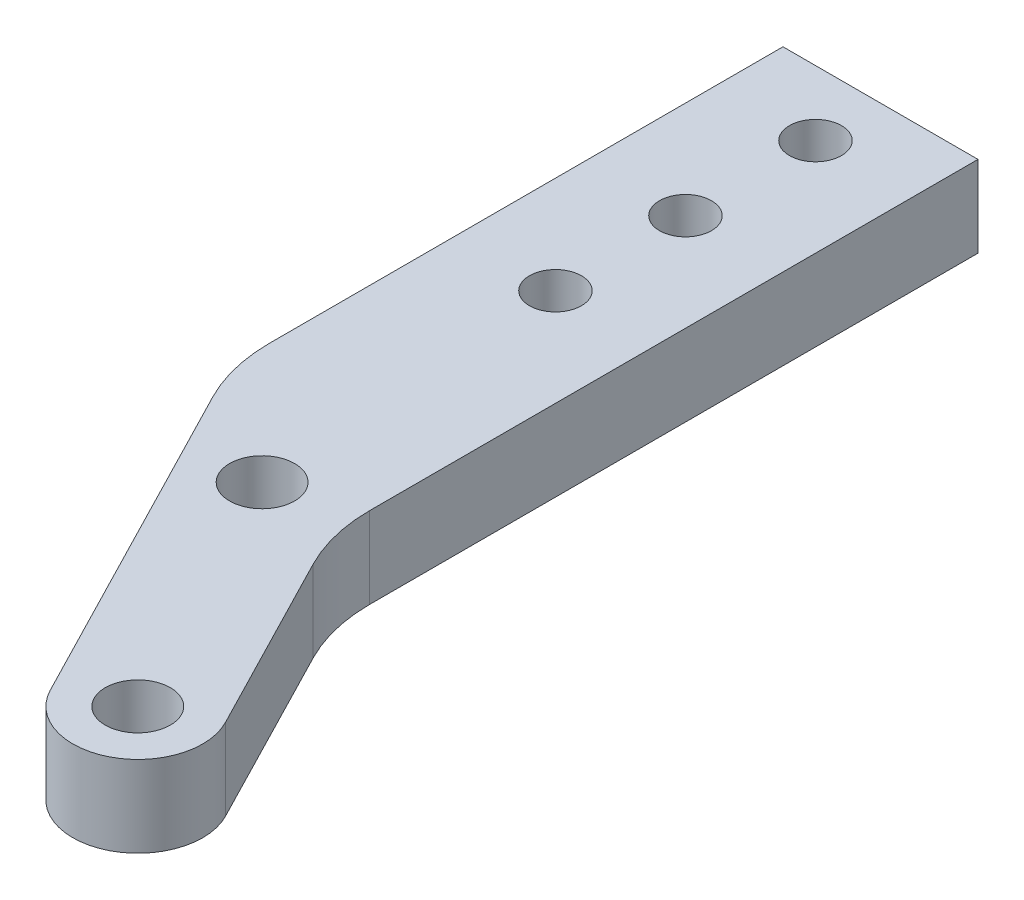
SolidWorks part; units mm, degrees
material "ABS"
ref_plane "Спереди" through (0, 0, 0) normal (0, 0, 1) x (1, 0, 0)
ref_plane "Сверху" through (0, 0, 0) normal (0, 1, 0) x (1, 0, 0)
ref_plane "Справа" through (0, 0, 0) normal (1, 0, 0) x (0, 0, -1)
ref_plane "Плоскость4" through (0, 0, 0) normal (0, -1, 0) x (1, 0, 0)
sketch "Эскиз1" plane through (0, 0, 0) normal (0, -1, 0) x (1, 0, 0)
  line L0 (-6, 31.6133) -> (-6, 0)
  line L1 (-6, 0) -> (6, 0)
  line L2 (6, 0) -> (6, 37.4366)
  line L3 (7.1106, 42.0169) -> (12.8562, 53.1679)
  line L4 (5.7447, 56.8321) -> (-4.8894, 36.1936)
  line L5 (9.3005, 55) -> (-19.6844, 55) construction
  line L6 (1.1765, 39.2331) -> (-19.6844, 39.2331) construction
  line L7 (0, 20) -> (-19.6844, 20) construction
  line L8 (0, 12) -> (-19.6844, 12) construction
  line L9 (0, 4) -> (-19.6844, 4) construction
  line L10 (9.3005, 59) -> (-19.6844, 59) construction
  line L11 (0, 0) -> (0, 105.7278) construction
  line L12 (9.3005, 55) -> (9.3005, 65.5898) construction
  arc A0 (6, 37.4366) -> (7.1106, 42.0169) centre (16, 37.4366) cw
  arc A1 (12.8562, 53.1679) -> (5.7447, 56.8321) centre (9.3005, 55) ccw
  arc A2 (-4.8894, 36.1936) -> (-6, 31.6133) centre (4, 31.6133) ccw
  dimension "D11" = 9.3005
  dimension "D14" = 10
  dimension "D15" = 10
  dimension "D16" = 4
  dimension "D1" = 31.6133
  dimension "D2" = 23.2171
  dimension "D3" = 37.4366
  dimension "D4" = 12
  dimension "D5" = 59
  dimension "D6" = 15.7669
  dimension "D7" = 8
  dimension "D8" = 8
  dimension "D9" = 12.5442
  dimension "D10" = 4
  dimension "D17" = 6
  dimension "D18" = 1.1765
  dimension "D19" = 4
extrude "Бобышка-Вытянуть1" add sketch "Эскиз1" against normal blind 5
sketch "Эскиз5" plane through (0, 0, 0) normal (0, -1, 0) x (1, 0, 0)
  line L0 (0, 55) -> (9.3, 55) construction
  line L1 (0, 0) -> (0, 65.2638) construction
  line L2 (-6, 4) -> (-6, 12) construction
  line L3 (-6, 31.6133) -> (-6, 0) construction
  line L4 (-6, 4) -> (6, 4) construction
  line L5 (-6, 12) -> (6, 12) construction
  line L6 (-6, 12) -> (-6, 20) construction
  line L7 (-6, 20) -> (6, 20) construction
  line L8 (9.3005, 59) -> (0, 59) construction
  line L9 (1.1809, 39.2315) -> (-10.9443, 39.2315) construction
  arc A0 (12.8562, 53.1679) -> (5.7447, 56.8321) centre (9.3005, 55) ccw construction
  dimension "D1" = 4
  dimension "D2" = 15.7685
  dimension "D3" = 1.1809
hole_wizard "Диаметр отверстия A (0.234)3" positions "Трехмерный эскиз6" profile "Эскиз8" hole size "A" standard "Ansi Inch"
sketch3d "Трехмерный эскиз6"
  line L0 (-6, 0, 4) -> (6, 0, 4) construction
  line L1 (0, 0, 0) -> (0, 0, 65.2638) construction
  line L2 (-6, 0, 20) -> (6, 0, 20) construction
  point P0 (0, 0, 4)
  point P5 (0, 0, 4)
  point P7 (0, 0, 4)
  point P11 (0, 0, 20)
  point P15 (0, 0, 32.6319)
sketch "Эскиз8" plane through (0, 0, 4) normal (1, 0, 0) x (0, 0, -1)
  line L0 (0, 0) -> (0, 5)
  line L1 (0, 5) -> (1.6, 5)
  line L2 (1.6, 5) -> (1.6, 0)
  line L5 (1.6, 0) -> (0, 0)
  line L11 (0, -6.35) -> (0, 107.95) construction
  dimension "Диаметр сквозного отверстия" = 3.2
  dimension "Глубина сквозного отверстия" = 5
pattern_linear "Линейный массив1" count 3 spacing 8 along (0, 0, 1) of "Диаметр отверстия A (0.234)3"
hole_wizard "Диаметр отверстия A (0.234)4" positions "Трехмерный эскиз8" profile "Эскиз10" hole size "A" standard "Ansi Inch" end condition through all
sketch3d "Трехмерный эскиз8"
  point P0 (9.3, 0, 55)
  point P3 (1.1809, 0, 39.2315)
sketch "Эскиз10" plane through (9.3, 0, 55) normal (1, 0, 0) x (0, 0, -1)
  line L0 (0, 0) -> (0, 5)
  line L1 (0, 5) -> (2, 5)
  line L2 (2, 5) -> (2, 0)
  line L5 (2, 0) -> (0, 0)
  line L11 (0, -6.35) -> (0, 107.95) construction
  dimension "Диаметр сквозного отверстия" = 4
  dimension "Глубина сквозного отверстия" = 5
